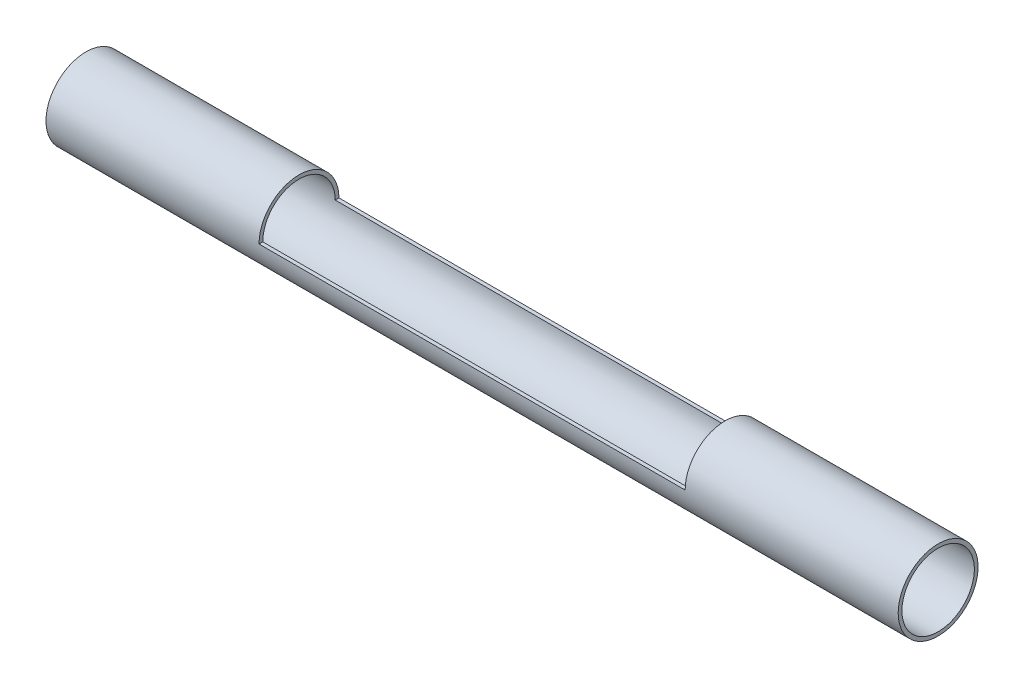
SolidWorks part; units mm, degrees
ref_plane "Front Plane" through (0, 0, 0) normal (0, 0, 1) x (1, 0, 0)
ref_plane "Top Plane" through (0, 0, 0) normal (0, 1, 0) x (1, 0, 0)
ref_plane "Right Plane" through (0, 0, 0) normal (1, 0, 0) x (0, 0, -1)
sketch "Sketch1" plane through (0, 0, 0) normal (0, 1, 0) x (1, 0, 0)
  line L0 (0, 0) -> (203.2, 0) construction
  line L1 (0, 9.525) -> (203.2, 9.525)
  line L2 (203.2, 9.525) -> (203.2, 8.636)
  line L3 (203.2, 8.636) -> (0, 8.636)
  line L4 (0, 8.636) -> (0, 9.525)
  dimension "D1" = 203.2
  dimension "D2" = 9.525
  dimension "D3" = 0.889
revolve "Revolve1" add sketch "Sketch1" angle 360 about L0
sketch "Sketch2" plane through (0, 0, 0) normal (0, 0, 1) x (1, 0, 0)
  line L0 (0, 9.525) -> (0, -9.525) construction
  line L1 (50.8, 16.7214) -> (152.4, 16.7214)
  line L2 (50.8, 16.7214) -> (50.8, 0)
  line L3 (50.8, 0) -> (152.4, 0)
  line L4 (152.4, 16.7214) -> (152.4, 0)
  line L5 (203.2, 9.525) -> (0, 9.525) construction
  dimension "D1" = 101.6
  dimension "D2" = 50.8
  dimension "D3" = 9.525
extrude "Cut-Extrude1" cut sketch "Sketch2" against normal through all and the other way through all
